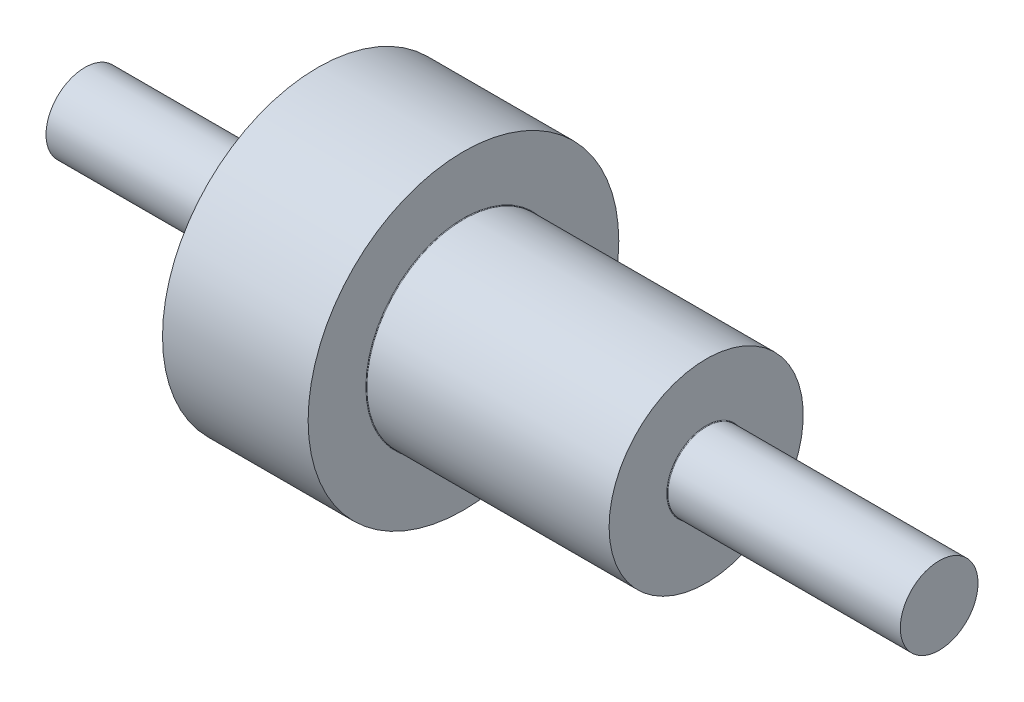
SolidWorks part; units mm, degrees
ref_plane "Alzado" through (0, 0, 0) normal (0, 0, 1) x (1, 0, 0)
ref_plane "Planta" through (0, 0, 0) normal (0, 1, 0) x (1, 0, 0)
ref_plane "Vista lateral" through (0, 0, 0) normal (1, 0, 0) x (0, 0, -1)
sketch "Croquis1" plane through (0, 0, 0) normal (0, 0, 1) x (1, 0, 0)
  line L0 (0, 0) -> (28, 0) construction
  line L1 (0, 0) -> (0, 2)
  line L2 (0, 2) -> (4, 2)
  line L3 (4, 2) -> (4, 8)
  line L4 (4, 8) -> (11.5, 8)
  line L5 (28, 0) -> (28, 2)
  line L6 (28, 2) -> (24, 2)
  line L7 (24, 2) -> (24, 5)
  line L8 (24, 5) -> (11.5, 5)
  line L9 (11.5, 5) -> (11.5, 8)
  line L10 (0, 0) -> (28, 0)
  dimension "D1" = 2
  dimension "D2" = 12.5
  dimension "D3" = 4
  dimension "D4" = 8
  dimension "D5" = 4
  dimension "D6" = 28
  dimension "D7" = 2
  dimension "D8" = 5
revolve "Revolución1" add sketch "Croquis1" angle 360 about L0
sketch "Croquis2" plane through (0, 0, 0) normal (-1, 0, 0) x (0, 0, 1)
  circle A0 centre (0, 0) radius 2
extrude "Saliente-Extruir1" add sketch "Croquis2" along normal blind 8
sketch "Croquis3" plane through (28, 0, 0) normal (1, 0, 0) x (0, 0, -1)
  circle A0 centre (0, 0) radius 2
extrude "Saliente-Extruir2" add sketch "Croquis3" along normal blind 8
fillet "Redondeo1" radius 0.03 1 edges at (4, 0, 2)
fillet "Redondeo2" radius 0.03 2 edges at (24, 0, 2) (11.5, 0, 5)
